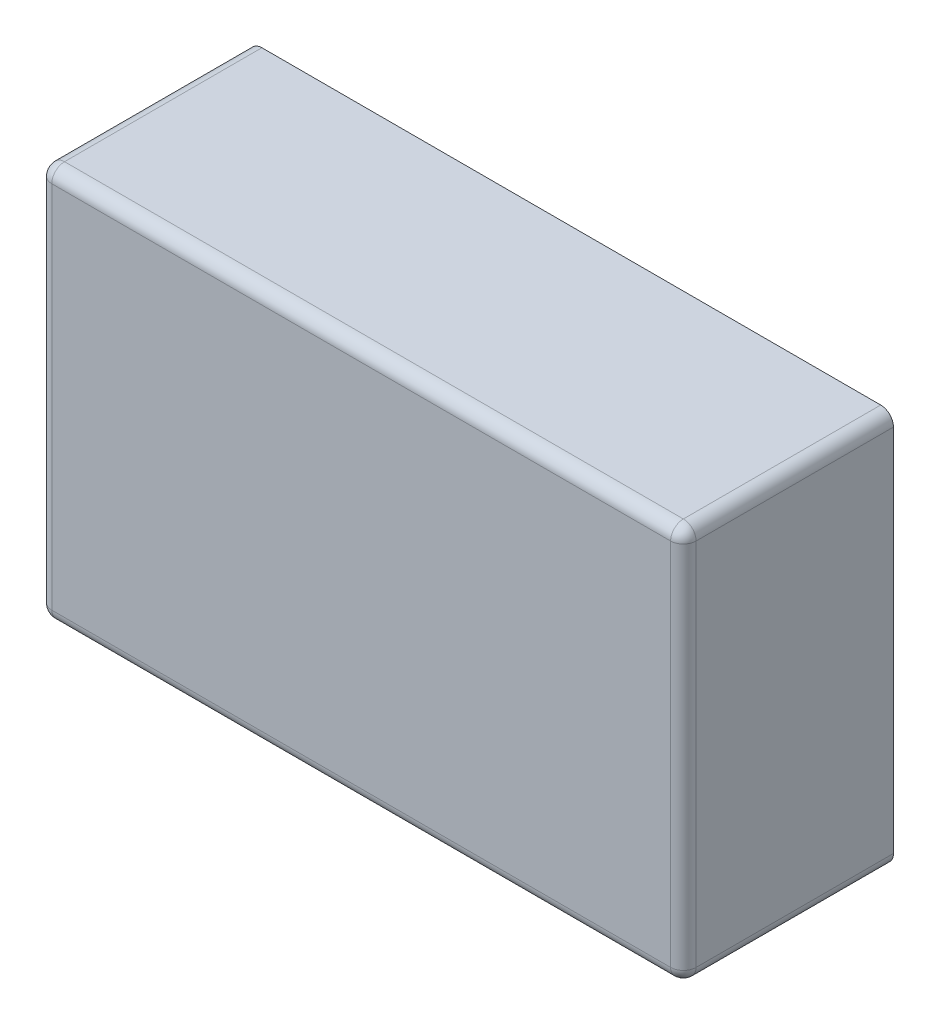
SolidWorks part; units mm, degrees
material "Plain Carbon Steel"
ref_plane "Front Plane" through (0, 0, 0) normal (0, 0, 1) x (1, 0, 0)
ref_plane "Top Plane" through (0, 0, 0) normal (0, 1, 0) x (1, 0, 0)
ref_plane "Right Plane" through (0, 0, 0) normal (1, 0, 0) x (0, 0, -1)
sketch "Sketch1" plane through (0, 0, 0) normal (0, 0, 1) x (1, 0, 0)
  line L1 (0, 0) -> (253, 0)
  line L2 (0, 0) -> (0, 155)
  line L3 (0, 155) -> (253, 155)
  line L4 (253, 0) -> (253, 155)
  dimension "D1" = 253
  dimension "D2" = 155
extrude "Boss-Extrude1" add sketch "Sketch1" along normal blind 82.5 contours L2 L3 L4 L1
fillet "Fillet1" radius 5 8 edges at (253, 77.5, 82.5) (126.5, 155, 82.5) (0, 77.5, 82.5) (126.5, 0, 82.5) (0, 155, 41.25) (253, 155, 41.25) (253, 0, 41.25) (0, 0, 41.25)
sketch "Sketch2" plane through (0, 0, 0) normal (0, 0, -1) x (-1, 0, 0)
  line L12 (-2, 5) -> (-2, 150)
  line L13 (-5, 153) -> (-248, 153)
  line L14 (-251, 150) -> (-251, 5)
  line L15 (-248, 2) -> (-5, 2)
  line L16 (-2, 5) -> (-2, 150)
  line L17 (-5, 153) -> (-248, 153)
  line L18 (-251, 150) -> (-251, 5)
  line L19 (-248, 2) -> (-5, 2)
  arc A12 (-2, 150) -> (-5, 153) centre (-5, 150) ccw
  arc A13 (-248, 153) -> (-251, 150) centre (-248, 150) ccw
  arc A14 (-251, 5) -> (-248, 2) centre (-248, 5) ccw
  arc A15 (-5, 2) -> (-2, 5) centre (-5, 5) ccw
  arc A16 (-2, 150) -> (-5, 153) centre (-5, 150) ccw
  arc A17 (-248, 153) -> (-251, 150) centre (-248, 150) ccw
  arc A18 (-251, 5) -> (-248, 2) centre (-248, 5) ccw
  arc A19 (-5, 2) -> (-2, 5) centre (-5, 5) ccw
  dimension "D1" = 2
extrude "Cut-Extrude1" cut sketch "Sketch2" against normal blind 6.3
ref_plane "Plane1" through (0, 5, 0) normal (0, 1, 0) x (1, 0, 0)
sketch "Sketch5" plane through (0, 0, 0) normal (-1, 0, 0) x (0, 0, 1)
  line L0 (0, 5) -> (0, 150) construction
  line L1 (0, 20.5) -> (45, 20.5)
  line L2 (0, 20.5) -> (0, 134.5)
  line L3 (0, 134.5) -> (45, 134.5)
  line L4 (45, 20.5) -> (45, 134.5)
  line L5 (0, 155) -> (77.5, 155) construction
  dimension "D1" = 114
  dimension "D2" = 45
  dimension "D3" = 20.5
extrude "Boss-Extrude2" add sketch "Sketch5" along normal blind 12.7 contours L4 L3 L2 L1
fillet "Fillet2" radius 3 2 edges at (-12.7, 134.5, 22.5) (-12.7, 20.5, 22.5)
ref_plane "Plane2" through (0, 77.5, 0) normal (0, -1, 0) x (-1, 0, 0)
